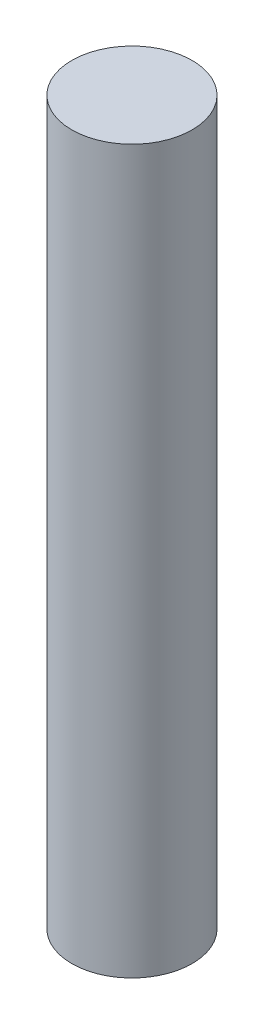
SolidWorks part; units mm, degrees
material "Balsa"
ref_plane "Front Plane" through (0, 0, 0) normal (0, 0, 1) x (1, 0, 0)
ref_plane "Top Plane" through (0, 0, 0) normal (0, 1, 0) x (1, 0, 0)
ref_plane "Right Plane" through (0, 0, 0) normal (1, 0, 0) x (0, 0, -1)
sketch "Sketch1" plane through (0, 0, 0) normal (0, 1, 0) x (1, 0, 0)
  circle A0 centre (0, 0) radius 3.175
  dimension "D1" = 6.35
extrude "Boss-Extrude1" add sketch "Sketch1" along normal mid plane 38.1
